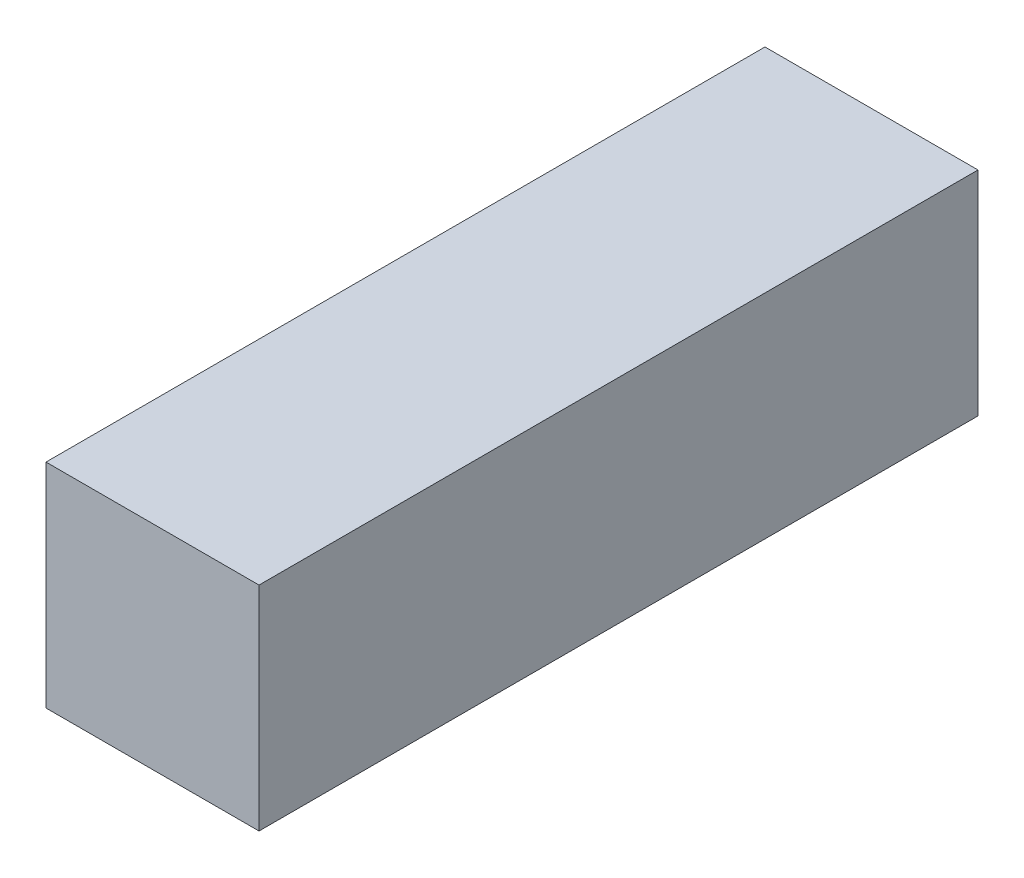
SolidWorks part; units mm, degrees
material "AISI 1020"
ref_plane "Спереди" through (0, 0, 0) normal (0, 0, 1) x (1, 0, 0)
ref_plane "Сверху" through (0, 0, 0) normal (0, 1, 0) x (1, 0, 0)
ref_plane "Справа" through (0, 0, 0) normal (1, 0, 0) x (0, 0, -1)
sketch "Эскиз1" plane through (0, 0, 0) normal (0, 0, 1) x (1, 0, 0)
  line L0 (-11.3137, -4) -> (-8, -4) construction
  line L1 (-8, 4) -> (-16, 4)
  line L2 (-8, 4) -> (-8, -4)
  line L3 (-8, -4) -> (-16, -4)
  line L4 (-16, 4) -> (-16, -4)
extrude "Бобышка-Вытянуть1" add sketch "Эскиз1" along normal up to surface (27 mm away)
